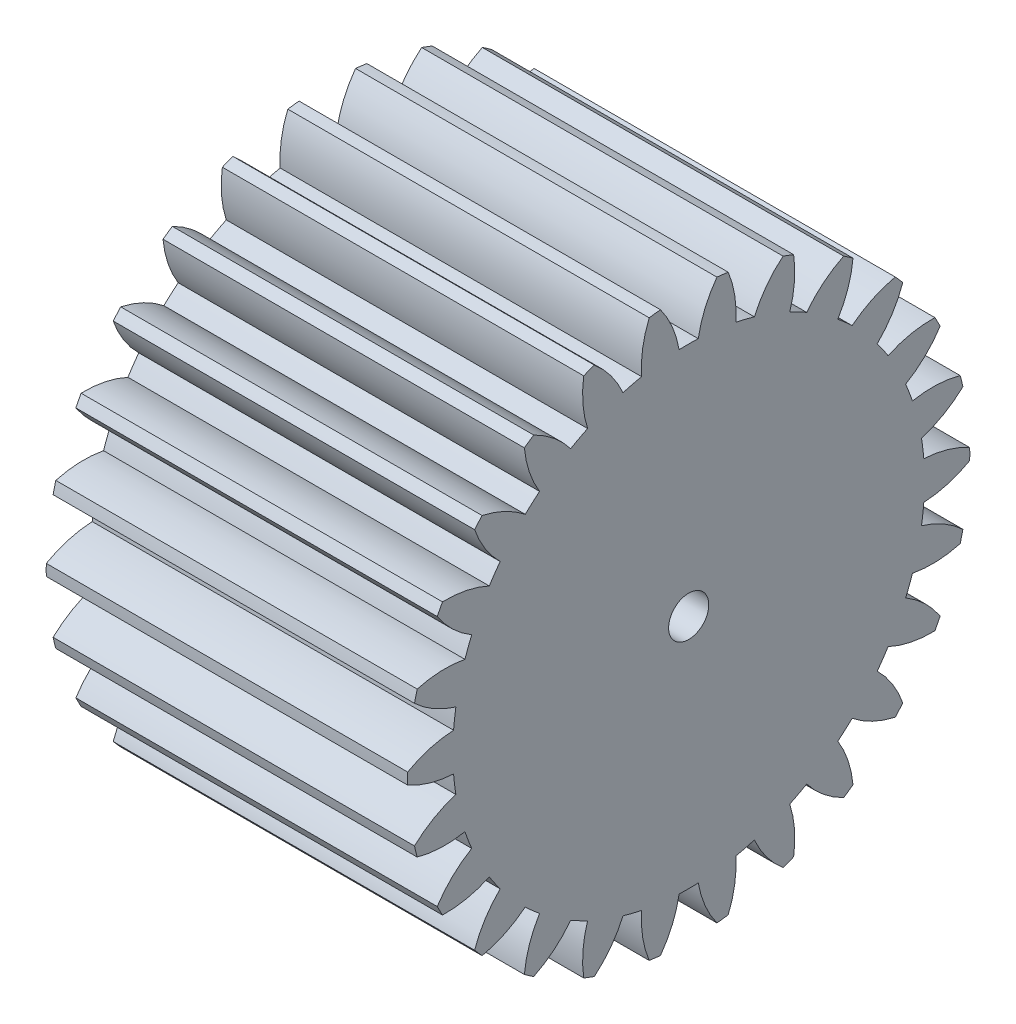
SolidWorks part; units mm, degrees
ref_plane "Plane1" through (0, 0, 0) normal (0, 0, 1) x (1, 0, 0)
ref_plane "Plane2" through (0, 0, 0) normal (0, 1, 0) x (1, 0, 0)
ref_plane "Plane3" through (0, 0, 0) normal (1, 0, 0) x (0, 0, -1)
other "Configuration Table"
sketch "HoldingSke" plane through (0, 0, 0) normal (0, 1, 0) x (1, 0, 0)
  line L0 (0, 0) -> (1.7976, -0.8767)
  line L1 (-15, 0) -> (100, 0) construction
  line L2 (0, 0) -> (-2.1039, 2.3779)
  line L3 (0, 0) -> (-11.863, 4.5341)
  line L4 (0, 0) -> (7.762, 3.7858)
  line L5 (0, 0) -> (-46.8476, -17.4728)
  line L6 (0, 0) -> (-7.4607, -5.0337)
  line L7 (-2.1039, 2.3779) -> (8.6586, 51.2059)
  line L8 (-76.2, 54.61) -> (-76.1, 54.61)
  line L9 (-71.009, 38.7566) -> (-53.1078, 45.2721)
  line L10 (-76.2, 71.12) -> (104.1128, 71.12)
  line L11 (0, 0) -> (-9, 0)
  line L12 (-76.2, 101.6) -> (-76.181, 101.6)
  line L13 (24.9733, 27.94) -> (52.9518, 28.4284)
  line L14 (24.9733, 27.94) -> (24.9743, 27.94)
  line L15 (24.9733, 27.94) -> (100.4006, 29.5858)
  line L16 (-63.627, -0.5) -> (-12.827, -0.5)
  circle A0 centre (0, 0) radius 0.5
  circle A1 centre (0, 0) radius 5.874
  circle A2 centre (0, 0) radius 37.5
  circle A3 centre (0, 0) radius 0.5
  dimension "MHD" = 11.748
  dimension "Hub_dia" = 75
  dimension "Bore" = 1
  dimension "MBD" = 1
  dimension "Num_teeth" = 26
  dimension "Pitch" = 2
  dimension "Overall_len" = 50
  dimension "Show_teeth" = 26
  dimension "Thickness" = 9
  dimension "OAL" = 50.0001
  dimension "T_dim" = 0.1
  dimension "Ap" = 20
  dimension "H" = 19.05
  dimension "Pitch_radius" = 180.3128
  dimension "Width" = 9
  dimension "Backlash" = 0.019
  dimension "Addendum_fac" = 1
  dimension "Dedendum_fac" = 1.25
  dimension "Clearance_fac" = 0.25
  dimension "Dedendum_add" = 0.001
  dimension "Module" = 0.5
sketch "BasProSke" plane through (0, 0, 0) normal (0, 1, 0) x (1, 0, 0)
  line L0 (-10, 0) -> (60, 0) construction
  line L1 (0, 0) -> (0, 7)
  line L2 (0, 0) -> (9, 0)
  line L3 (9, 0) -> (9, 7)
  line L4 (9, 7) -> (0, 7)
  dimension "Thickness" = 9
  dimension "Diameter" = 14
revolve "Base-Revolve" add sketch "BasProSke" angle 360 about L0
sketch "TooCutSke" plane through (0, 0, 0) normal (1, 0, 0) x (0, 0, -1)
  line L1 (0, 0) -> (0, 107) construction
  line L2 (0, 0) -> (-0.4257, 6.486) construction
  line L3 (0, 0) -> (-1.5646, 12.8855) construction
  line L4 (-0.4257, 6.486) -> (-0.7823, 6.4427) construction
  arc A0 (0.2384, 5.8692) -> (-0.2384, 5.8692) centre (0, 0) ccw
  arc A1 (0.7209, 6.9883) -> (-0.7209, 6.9883) centre (0, 0) ccw
  circle A2 centre (0, 0) radius 6.5 construction
  circle A3 centre (0, 0) radius 6.108 construction
  arc A4 (-0.2384, 5.8692) -> (-0.7209, 6.9883) centre (-2.8007, 5.4281) ccw
  arc A5 (0.7209, 6.9883) -> (0.2384, 5.8692) centre (2.8007, 5.4281) ccw
  dimension "Root_dia" = 11.748
  dimension "Overcut_dia" = 14.0508
  dimension "Pitch_dia" = 13
  dimension "Base_dia" = 12.216
  dimension "Flank_rad" = 2.6
  dimension "Half_ang" = 6.923
  dimension "Half_CT" = 0.3592
extrude "ToothCut" cut sketch "TooCutSke" along normal through all
fillet "Breaks" [suppressed] radius 0.01
fillet "RootFillets" [suppressed] radius 0.126
pattern_circular "TeethCuts" count 26 every 13.846 about axis through (-10, 0, 0) along (1, 0, 0) of "ToothCut", "RootFillets", "Breaks"
sketch "HubNeaOneSke" plane through (0, 0, 0) normal (-1, 0, 0) x (0, 0, 1)
  circle A0 centre (0, 0) radius 5.874
  dimension "Diameter" = 11.748
extrude "HubNearOne" [suppressed] add sketch "HubNeaOneSke" along normal blind 41.0001
sketch "HubNeaBotSke" plane through (0, 0, 0) normal (-1, 0, 0) x (0, 0, 1)
  circle A0 centre (0, 0) radius 5.874
  dimension "Diameter" = 11.748
extrude "HubNearBoth" [suppressed] add sketch "HubNeaBotSke" along normal blind 20.5
ref_plane "FarPln" through (9, 0, 0) normal (1, 0, 0) x (0, 0, -1)
sketch "HubFarSke" plane through (9, 0, 0) normal (1, 0, 0) x (0, 0, -1)
  circle A0 centre (0, 0) radius 5.874
  dimension "Diameter" = 11.748
extrude "HubFar" [suppressed] add sketch "HubFarSke" along normal blind 20.5
sketch "BorSke" plane through (0, 0, 0) normal (1, 0, 0) x (0, 0, -1)
  circle A0 centre (0, 0) radius 0.5
  dimension "Diameter" = 1
extrude "Bore" cut sketch "BorSke" along normal mid plane 100.0001
sketch "KeySke" plane through (0, 0, 0) normal (1, 0, 0) x (0, 0, -1)
  line L0 (-0.05, 0) -> (-0.05, 0.6)
  line L1 (-0.05, 0.6) -> (0.05, 0.6)
  line L2 (0.05, 0.6) -> (0.05, 0)
  line L3 (0, 0) -> (0, 34) construction
  line L4 (-0.05, 0) -> (0.05, 0)
  dimension "Offset" = 0.6
  dimension "Width" = 0.1
extrude "Keyway" [suppressed] cut sketch "KeySke" along normal mid plane 100.0001
pattern_circular "Keyway2" [suppressed] count 2 every 90 about axis through (-10, 0, 0) along (1, 0, 0)
equation "' \"Module@HoldingSke\" = 6.35"
equation "' \"Num_teeth@HoldingSke\" = 12"
equation "' \"Ap@HoldingSke\" =  20"
equation "' \"Ap@HoldingSke\" = 20"
equation "' \"Width@HoldingSke\" = 0.5 * 25.4"
equation "' \"Hub_dia@HoldingSke\"= 1 * 25.4"
equation "' \"Hub_dia@HoldingSke\" = 1 * 25.4"
equation "' \"Overall_len@HoldingSke\" = 1.0 * 25.4"
equation "' \"Bore@HoldingSke\" = 0.75 * 25.4"
equation "' \"T_dim@HoldingSke\" = 0.1 * 25.4"
equation "' \"Width@KeySke\" = 0.25 * 25.4"
equation "' \"Show_teeth@HoldingSke\" = 13"
equation "' \"Backlash@HoldingSke\" = 0.009 * 25.4"
equation "' \"Addendum_fac@HoldingSke\" = 1.0"
equation "' \"Dedendum_fac@HoldingSke\" = 1.25"
equation "' \"Dedendum_add@HoldingSke\" = 0.00005 * 25.4"
equation "' \"Clearance_fac@HoldingSke\" = 0.25"
equation "\"Pitch@HoldingSke\" = 1 / \"Module@HoldingSke\""
equation "\"Overcut_dia@TooCutSke\" = (\"Num_teeth@HoldingSke\" + 2 * \"Addendum_fac@HoldingSke\") / \"Pitch@HoldingSke\" + 0.002 * 25.4"
equation "\"Pitch_dia@TooCutSke\" = \"Num_teeth@HoldingSke\" / \"Pitch@HoldingSke\""
equation "\"Base_dia@TooCutSke\" = \"Num_teeth@HoldingSke\" / \"Pitch@HoldingSke\" * cos((\"Ap@HoldingSke\"  * 3.14159265 / 180))"
equation "\"Root_dia@TooCutSke\" = (\"Num_teeth@HoldingSke\" + 2) / \"Pitch@HoldingSke\" - 2 * (\"Addendum_fac@HoldingSke\" + \"Dedendum_fac@HoldingSke\") / \"Pitch@HoldingSke\" - \"Dedendum_add@HoldingSke\" * 2"
equation "\"Half_ang@TooCutSke\" = 180 / \"Num_teeth@HoldingSke\""
equation "\"Half_CT@TooCutSke\" = \"Num_teeth@HoldingSke\" / \"Pitch@HoldingSke\" * sin((3.14159265 / 2 / \"Num_teeth@HoldingSke\")) / 2 - 7 * \"Backlash@HoldingSke\" / 4"
equation "\"Flank_rad@TooCutSke\" = \"Num_teeth@HoldingSke\" / \"Pitch@HoldingSke\" / 5"
equation "\"Radius@RootFillets\" = \"Clearance_fac@HoldingSke\" / \"Pitch@HoldingSke\" + \"Dedendum_add@HoldingSke\""
equation "\"Break_rad@Breaks\" = 0.02 / \"Pitch@HoldingSke\""
equation "\"Thickness@HoldingSke\" = \"Width@HoldingSke\""
equation "\"OAL@HoldingSke\" = \"Thickness@HoldingSke\""
equation "\"MHD@HoldingSke\" = (\"Num_teeth@HoldingSke\" + 2) / \"Pitch@HoldingSke\" - 2 * (\"Addendum_fac@HoldingSke\" + \"Dedendum_fac@HoldingSke\")  / \"Pitch@HoldingSke\" - \"Dedendum_add@HoldingSke\" * 2"
equation "\"MBD@HoldingSke\" = (\"Num_teeth@HoldingSke\" + 2) / \"Pitch@HoldingSke\" - 2 * (\"Addendum_fac@HoldingSke\" + \"Dedendum_fac@HoldingSke\")  / \"Pitch@HoldingSke\" - \"Dedendum_add@HoldingSke\" * 2 - 0.002 * 25.4"
equation "\"MHD@HoldingSke\" = ((sgn( \"MHD@HoldingSke\" - \"Hub_dia@HoldingSke\" )-1)*( \"MHD@HoldingSke\" - \"Hub_dia@HoldingSke\" ))/-2+ \"Hub_dia@HoldingSke\""
equation "\"MBD@HoldingSke\" = ((sgn( \"MBD@HoldingSke\" - \"Bore@HoldingSke\" )-1)*( \"MBD@HoldingSke\" - \"Bore@HoldingSke\" ))/-2+ \"Bore@HoldingSke\""
equation "\"OAL@HoldingSke\" = ((sgn( \"OAL@HoldingSke\" - \"Overall_len@HoldingSke\" )+1)*( \"OAL@HoldingSke\" - \"Overall_len@HoldingSke\" ))/2 + \"Overall_len@HoldingSke\" + 0.000002 * 25.4"
equation "\"Num_teeth@TeethCuts\" = int( \"Show_teeth@HoldingSke\" ) + 1"
equation "\"Num_teeth@TeethCuts\" = ((sgn( \"Num_teeth@TeethCuts\" - \"Num_teeth@HoldingSke\" )-1)*( \"Num_teeth@TeethCuts\" - \"Num_teeth@HoldingSke\" ))/-2+ \"Num_teeth@HoldingSke\""
equation "\"Num_teeth@TeethCuts\" = ((sgn( \"Num_teeth@TeethCuts\" - 2.0)+1)*( \"Num_teeth@TeethCuts\" - 2.0))/2 +2.0"
equation "\"Angle@TeethCuts\" = 360.0 / \"Num_teeth@HoldingSke\""
equation "\"Diameter@BasProSke\" = (\"Num_teeth@HoldingSke\" + 2 * \"Addendum_fac@HoldingSke\") / \"Pitch@HoldingSke\""
equation "\"Thickness@BasProSke\"  = \"Thickness@HoldingSke\""
equation "' \"Fillet_rad@BasProSke\" =  \"Thickness@HoldingSke\" * 0.05"
equation "' \"Fillet_rad@BasProSke\" = \"Thickness@HoldingSke\" * 0.05"
equation "\"MHD@HoldingSke\" = ((sgn( \"MHD@HoldingSke\" - \"Root_dia@TooCutSke\" )-1)*( \"MHD@HoldingSke\" - \"Root_dia@TooCutSke\" ))/-2+ \"Root_dia@TooCutSke\""
equation "\"Diameter@HubNeaOneSke\" = \"MHD@HoldingSke\""
equation "\"Length@HubNearOne\" = \"OAL@HoldingSke\" - \"Thickness@BasProSke\""
equation "\"Diameter@HubNeaBotSke\" = \"MHD@HoldingSke\""
equation "\"Length@HubNearBoth\" = ( \"OAL@HoldingSke\" - \"Thickness@BasProSke\" ) / 2.0"
equation "\"Thickness@FarPln\" = \"Thickness@BasProSke\""
equation "\"Diameter@HubFarSke\" = \"MHD@HoldingSke\""
equation "\"Length@HubFar\" = ( \"OAL@HoldingSke\" - \"Thickness@BasProSke\" ) / 2.0"
equation "\"Diameter@BorSke\" = \"MBD@HoldingSke\""
equation "\"D1@Bore\" = \"OAL@HoldingSke\" * 2.0"
equation "\"D1@Keyway\" = \"OAL@HoldingSke\" * 2.0"
equation "\"Offset@KeySke\" = \"T_dim@HoldingSke\" + \"MBD@HoldingSke\" / 2.0"
